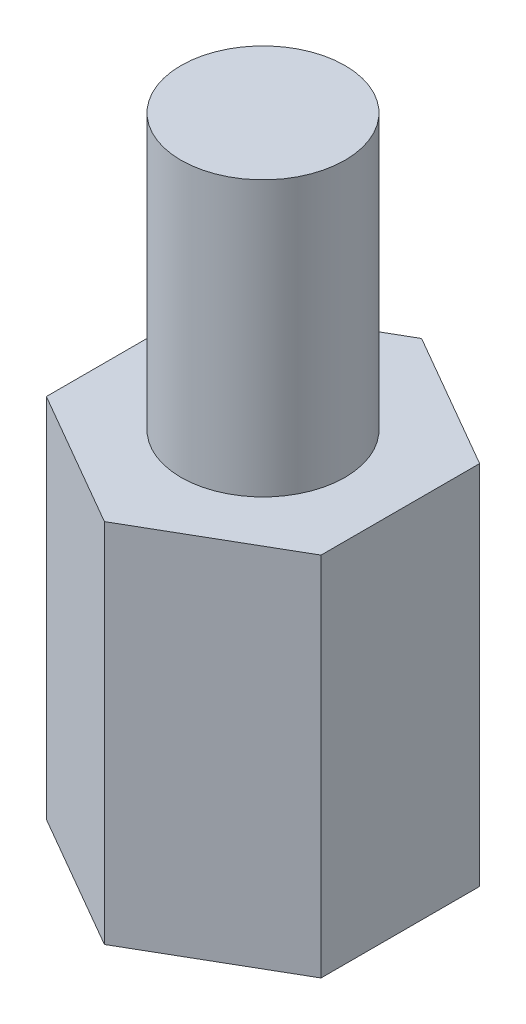
SolidWorks part; units mm, degrees
material "1060 Alloy"
ref_plane "Front Plane" through (0, 0, 0) normal (0, 0, 1) x (1, 0, 0)
ref_plane "Top Plane" through (0, 0, 0) normal (0, 1, 0) x (1, 0, 0)
ref_plane "Right Plane" through (0, 0, 0) normal (1, 0, 0) x (0, 0, -1)
sketch "Sketch1" plane through (0, 0, 0) normal (0, 1, 0) x (1, 0, 0)
  line L0 (0, 0) -> (0, -2.7496) construction
  line L1 (-2.3813, 1.3748) -> (-2.3812, -1.3748)
  line L2 (-2.3812, -1.3748) -> (0, -2.7496)
  line L3 (0, -2.7496) -> (2.3813, -1.3748)
  line L4 (2.3813, -1.3748) -> (2.3812, 1.3748)
  line L5 (2.3812, 1.3748) -> (0, 2.7496)
  line L6 (0, 2.7496) -> (-2.3813, 1.3748)
  circle A0 centre (0, 0) radius 2.3813 construction
  dimension "D1" = 4.7625
extrude "Boss-Extrude1" add sketch "Sketch1" along normal blind 6.35
sketch "Sketch2" plane through (0, 6.35, 0) normal (0, 1, 0) x (1, 0, 0)
  circle A0 centre (0, 0) radius 1.4224
  dimension "D1" = 2.8448
extrude "Boss-Extrude2" add sketch "Sketch2" along normal blind 4.7625
sketch "Sketch7" plane through (0, 0, 0) normal (0, -1, 0) x (1, 0, 0)
  circle A0 centre (0, 0) radius 1.4224
  dimension "D1" = 2.8448
extrude "Cut-Extrude4" cut sketch "Sketch7" against normal blind 4.7625
